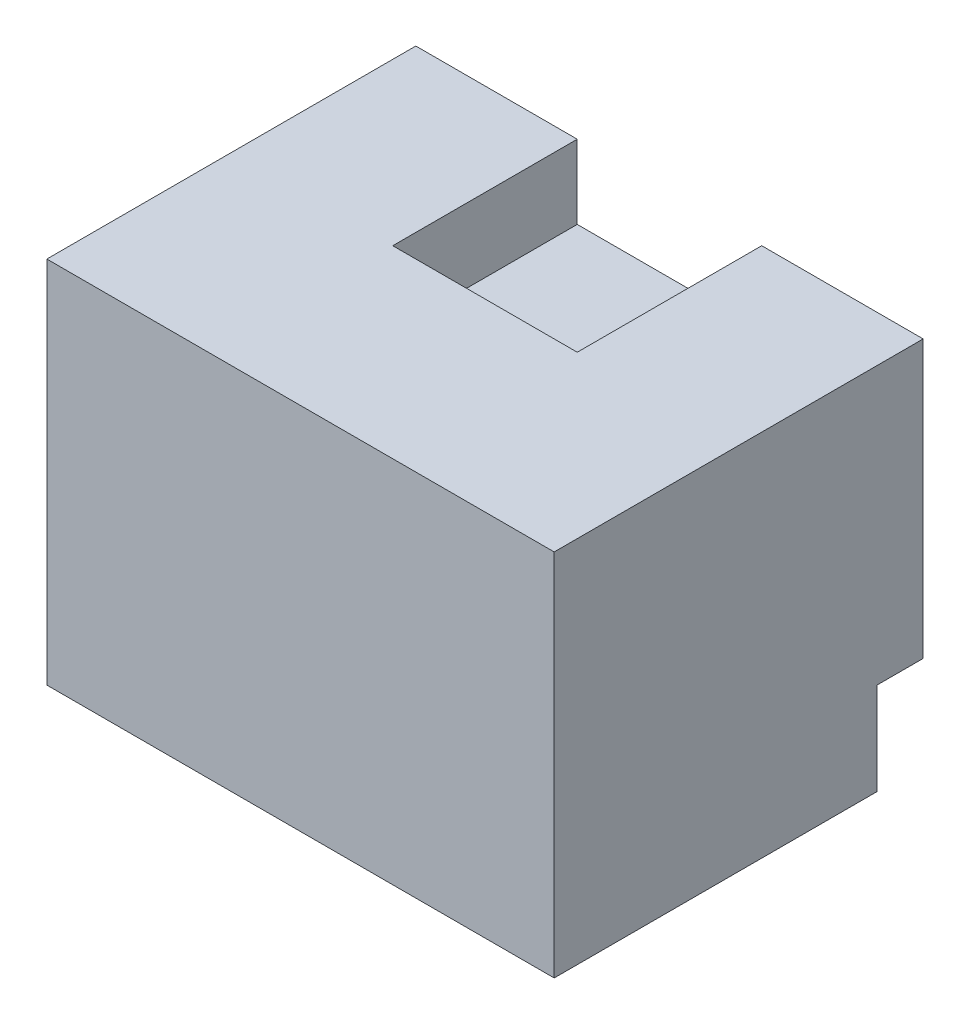
SolidWorks part; units mm, degrees
ref_plane "Front Plane" through (0, 0, 0) normal (0, 0, 1) x (1, 0, 0)
ref_plane "Top Plane" through (0, 0, 0) normal (0, 1, 0) x (1, 0, 0)
ref_plane "Right Plane" through (0, 0, 0) normal (1, 0, 0) x (0, 0, -1)
sketch "Sketch1" plane through (0, 0, 0) normal (0, 1, 0) x (1, 0, 0)
  line L1 (-27.5, 0) -> (27.5, 0)
  line L2 (-27.5, 0) -> (-27.5, -40)
  line L3 (-27.5, -40) -> (27.5, -40)
  line L4 (27.5, 0) -> (27.5, -40)
  line L7 (-10, 0) -> (10, 0)
  line L8 (10, 0) -> (10, -20)
  line L9 (10, -20) -> (-10, -20)
  line L10 (-10, -20) -> (-10, 0)
  point P0 (0, 0)
  dimension "D1" = 20
  dimension "D2" = 20
  dimension "D3" = 55
  dimension "D4" = 40
extrude "Boss-Extrude1" add sketch "Sketch1" along normal blind 30 contours L9 L10 L1 L2 L3 L4 L8
sketch "Sketch2" plane through (0, 0, 0) normal (0, -1, 0) x (1, 0, 0)
  line L1 (10, 20) -> (-10, 20)
  line L2 (10, 20) -> (10, 0)
  line L3 (10, 0) -> (-10, 0)
  line L4 (-10, 20) -> (-10, 0)
extrude "Boss-Extrude2" add sketch "Sketch2" against normal blind 22
sketch "Sketch3" plane through (0, 0, 0) normal (0, -1, 0) x (1, 0, 0)
  line L0 (-27.5, 0) -> (-27.5, 40) construction
  line L1 (27.5, 40) -> (-27.5, 40)
  line L2 (27.5, 40) -> (27.5, 5)
  line L3 (27.5, 5) -> (-27.5, 5)
  line L4 (-27.5, 40) -> (-27.5, 5)
  dimension "D1" = 35
extrude "Boss-Extrude3" add sketch "Sketch3" along normal blind 10
